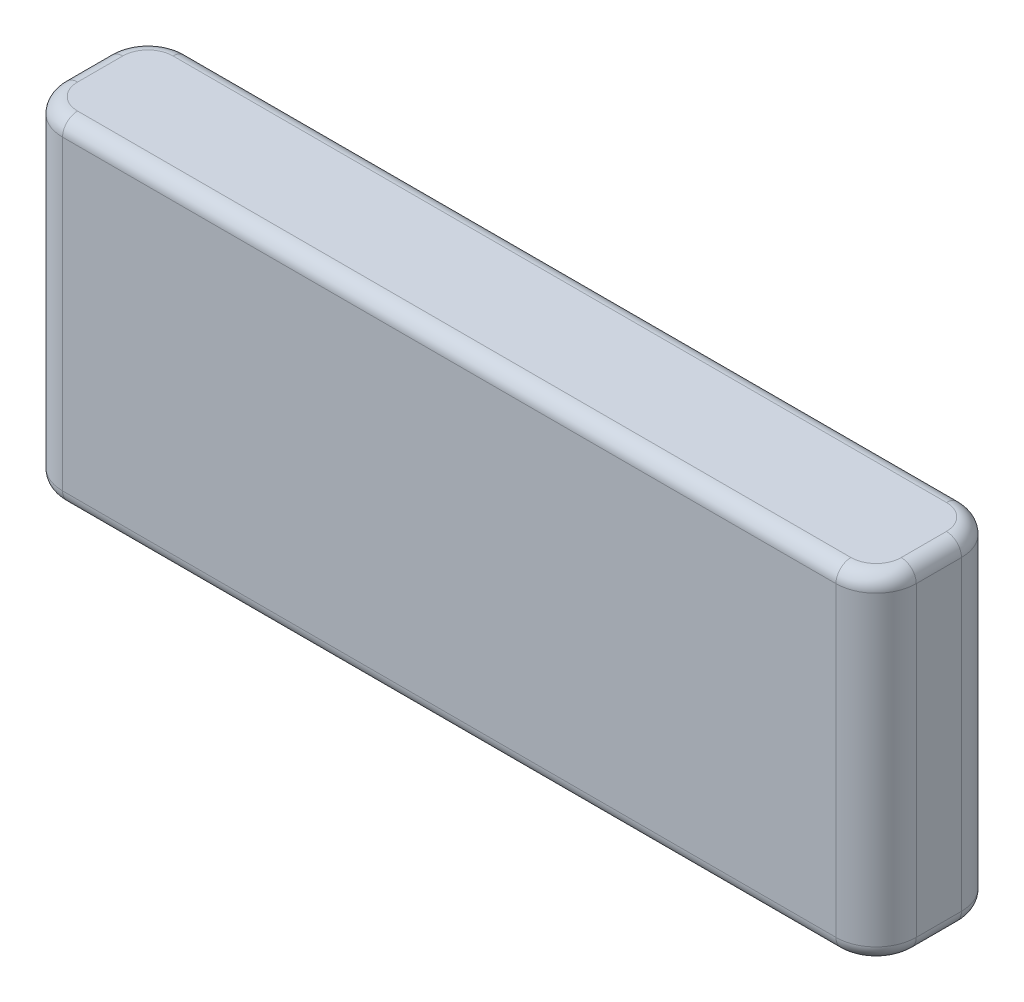
SolidWorks part; units mm, degrees
ref_plane "Front Plane" through (0, 0, 0) normal (0, 0, 1) x (1, 0, 0)
ref_plane "Top Plane" through (0, 0, 0) normal (0, 1, 0) x (1, 0, 0)
ref_plane "Right Plane" through (0, 0, 0) normal (1, 0, 0) x (0, 0, -1)
sketch "Sketch1" plane through (0, 0, 0) normal (0, 1, 0) x (1, 0, 0)
  line L1 (-85, -12.5) -> (85, -12.5)
  line L2 (-85, -12.5) -> (-85, 12.5)
  line L3 (-85, 12.5) -> (85, 12.5)
  line L4 (85, -12.5) -> (85, 12.5)
  point P4 (0, 12.5)
  point P6 (85, 0)
  dimension "D1" = 170
  dimension "D2" = 25
extrude "Boss-Extrude1" add sketch "Sketch1" along normal mid plane 67
fillet "Fillet1" radius 8 4 edges at (-85, 0, 12.5) (-85, 0, -12.5) (85, 0, -12.5) (85, 0, 12.5)
fillet "Fillet2" radius 3 16 edges at (82.6569, -33.5, 10.1569) (85, -33.5, 0) (82.6569, -33.5, -10.1569) (0, -33.5, -12.5) (-82.6569, -33.5, -10.1569) (-85, -33.5, 0) (-82.6569, -33.5, 10.1569) (0, -33.5, 12.5) (-82.6569, 33.5, -10.1569) (0, 33.5, -12.5) (82.6569, 33.5, -10.1569) (85, 33.5, 0) (82.6569, 33.5, 10.1569) (0, 33.5, 12.5) (-82.6569, 33.5, 10.1569) (-85, 33.5, 0)
